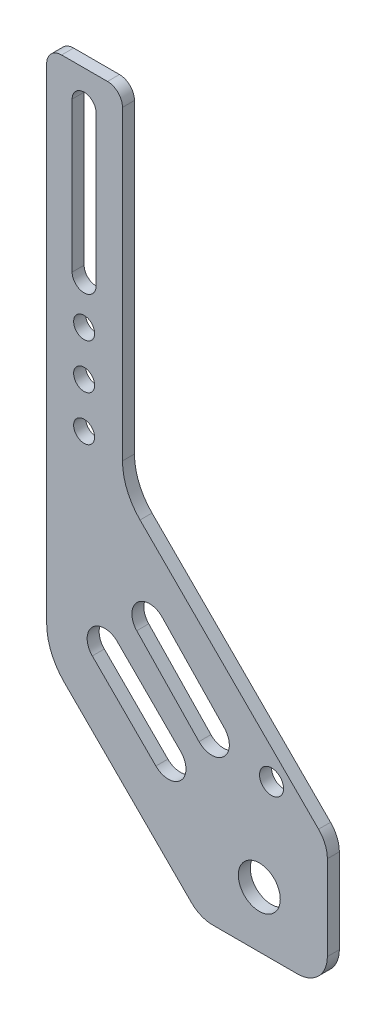
SolidWorks part; units mm, degrees
ref_plane "Front Plane" through (0, 0, 0) normal (0, 0, 1) x (1, 0, 0)
ref_plane "Top Plane" through (0, 0, 0) normal (0, 1, 0) x (1, 0, 0)
ref_plane "Right Plane" through (0, 0, 0) normal (1, 0, 0) x (0, 0, -1)
sketch "Sketch1" plane through (0, 0, 0) normal (0, 0, 1) x (1, 0, 0)
  line L0 (12.5, 119) -> (12.5, 69) construction
  line L2 (0, 5) -> (0, 125)
  line L3 (5, 130) -> (20.3018, 130)
  line L4 (25.3018, 22.8352) -> (25.3018, 125)
  line L5 (16.5, 119) -> (16.5, 69)
  line L6 (8.5, 119) -> (8.5, 69)
  line L7 (5.8579, -50.8579) -> (48.3088, -93.3088)
  line L8 (0, 5) -> (0, -36.7157)
  line L9 (90.7352, -50.8824) -> (31.1597, 8.6931)
  line L10 (57.6713, -17.8185) -> (90.7352, -50.8824)
  line L11 (60, 5) -> (60, -20.1472) construction
  line L12 (60, -20.1472) -> (93.6642, -53.8113) construction
  line L13 (0, 5) -> (0, -45) construction
  line L14 (0, -45) -> (51.2377, -96.2377) construction
  line L15 (19.3934, -34.3934) -> (40.6066, -55.6066) construction
  line L16 (23.5536, -30.2332) -> (44.7668, -51.4464)
  line L17 (15.2332, -38.5536) -> (36.4464, -59.7668)
  line L18 (34.1602, -40.8398) -> (57.6713, -17.8185) construction
  line L19 (55.3799, -96.2377) -> (83.6642, -96.2377)
  line L20 (34.3089, -19.7886) -> (55.0709, -41.4437) construction
  line L21 (30.0621, -23.8603) -> (50.824, -45.5154)
  line L22 (38.5557, -15.717) -> (59.3177, -37.372)
  line L23 (93.6642, -86.2377) -> (93.6642, -57.9535)
  arc A2 (20.3018, 130) -> (25.3018, 125) centre (20.3018, 125) cw
  arc A3 (5, 130) -> (0, 125) centre (5, 125) ccw
  arc A4 (16.5, 119) -> (8.5, 119) centre (12.5, 119) ccw
  arc A5 (8.5, 69) -> (16.5, 69) centre (12.5, 69) ccw
  circle A6 centre (12.5, 55) radius 3.5
  circle A7 centre (12.5, 40) radius 3.5
  circle A8 centre (12.5, 25) radius 3.5
  arc A9 (31.1597, 8.6931) -> (25.3018, 22.8352) centre (45.3018, 22.8352) cw
  arc A10 (0, -36.7157) -> (5.8579, -50.8579) centre (20, -36.7157) ccw
  arc A11 (23.5536, -30.2332) -> (15.2332, -38.5536) centre (19.3934, -34.3934) ccw
  arc A12 (36.4464, -59.7668) -> (44.7668, -51.4464) centre (40.6066, -55.6066) ccw
  arc A13 (30.0621, -23.8603) -> (38.5557, -15.717) centre (34.3089, -19.7886) cw
  arc A14 (59.3177, -37.372) -> (50.824, -45.5154) centre (55.0709, -41.4437) cw
  circle A15 centre (70.9538, -77.5131) radius 7
  circle A16 centre (75.0383, -45) radius 4
  arc A17 (93.6642, -57.9535) -> (90.7352, -50.8824) centre (83.6642, -57.9535) ccw
  arc A18 (48.3088, -93.3088) -> (55.3799, -96.2377) centre (55.3799, -86.2377) ccw
  arc A19 (83.6642, -96.2377) -> (93.6642, -86.2377) centre (83.6642, -86.2377) ccw
  point P5 (30, -45)
  point P7 (0, 0)
  point P16 (12.5, 94)
  point P46 (44.6899, -30.6162)
  dimension "D1" = 10
  dimension "D2" = 20
  dimension "D3" = 3
  dimension "D4" = 60
extrude "Boss-Extrude1" add sketch "Sketch1" along normal blind 4 contours L19 A19 L23 A17 L9 A9 L4 A2 L3 A3 L2 L8 A10 L7 A18 L22 A14 L21 A13 A5 L6 A4 L5 A6 A7 A8 A12 L17 A11 L16 A15 A16
